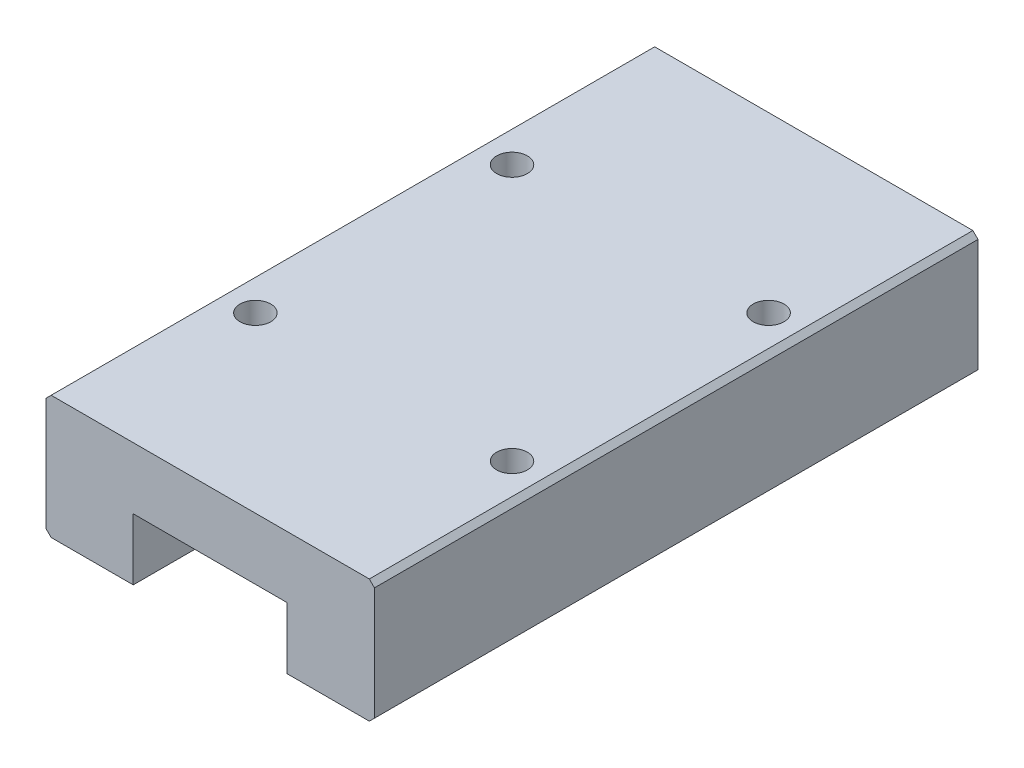
SolidWorks part; units mm, degrees
ref_plane "前视基准面" through (0, 0, 0) normal (0, 0, 1) x (1, 0, 0)
ref_plane "上视基准面" through (0, 0, 0) normal (0, 1, 0) x (1, 0, 0)
ref_plane "右视基准面" through (0, 0, 0) normal (1, 0, 0) x (0, 0, -1)
sketch "草图1" plane through (0, 0, 0) normal (0, 0, 1) x (1, 0, 0)
  line L0 (10.7676, -1.5211) -> (18.7676, -1.5211)
  line L1 (-12.2324, 10.4789) -> (18.7676, 10.4789)
  line L2 (-12.7324, 9.9789) -> (-12.7324, -1.0211)
  line L3 (-12.2324, -1.5211) -> (-4.2324, -1.5211)
  line L4 (19.2676, 9.9789) -> (19.2676, -1.0211)
  line L5 (-4.2324, -1.5211) -> (-4.2324, 4.4789)
  line L6 (10.7676, -1.5211) -> (10.7676, 4.4789)
  line L7 (-12.7324, 9.9789) -> (-12.2324, 10.4789)
  line L8 (-4.2324, 4.4789) -> (10.7676, 4.4789)
  line L9 (18.7676, 10.4789) -> (19.2676, 9.9789)
  line L10 (19.2676, -1.0211) -> (18.7676, -1.5211)
  line L11 (-12.7324, -1.0211) -> (-12.2324, -1.5211)
  line L12 (18.7676, 10.4789) -> (-12.2324, 10.4789) construction
  line L13 (18.7676, 10.4789) -> (-12.2324, 10.4789) construction
  point P0 (-12.7324, 10.4789)
  point P1 (19.2676, -1.5211)
  point P2 (-12.7324, -1.5211)
  point P3 (19.2676, 10.4789)
  dimension "D1" = 32
  dimension "D2" = 12
extrude "凸台-拉伸2" add sketch "草图1" along normal blind 58.8
sketch "草图2" plane through (0, 10.4789, 0) normal (0, 1, 0) x (1, 0, 0)
  line L1 (-22.2827, -29.4) -> (-9.2324, -29.4)
  line L4 (-22.2827, -41.9) -> (-10.7324, -41.9)
  line L9 (-10.7324, -16.9) -> (-22.8447, -16.9)
  circle A0 centre (-9.2324, -41.9) radius 1.5
  circle A1 centre (-9.2324, -16.9) radius 1.5
  circle A2 centre (15.7676, -41.9) radius 1.5
  circle A3 centre (15.7676, -16.9) radius 1.5
  dimension "D5" = 3
  dimension "D6" = 3
  dimension "D7" = 3
  dimension "D8" = 3
  dimension "D1" = 12.5
extrude "切除-拉伸1" cut sketch "草图2" against normal blind 4 contours A0 | A1 | A3 | A2
